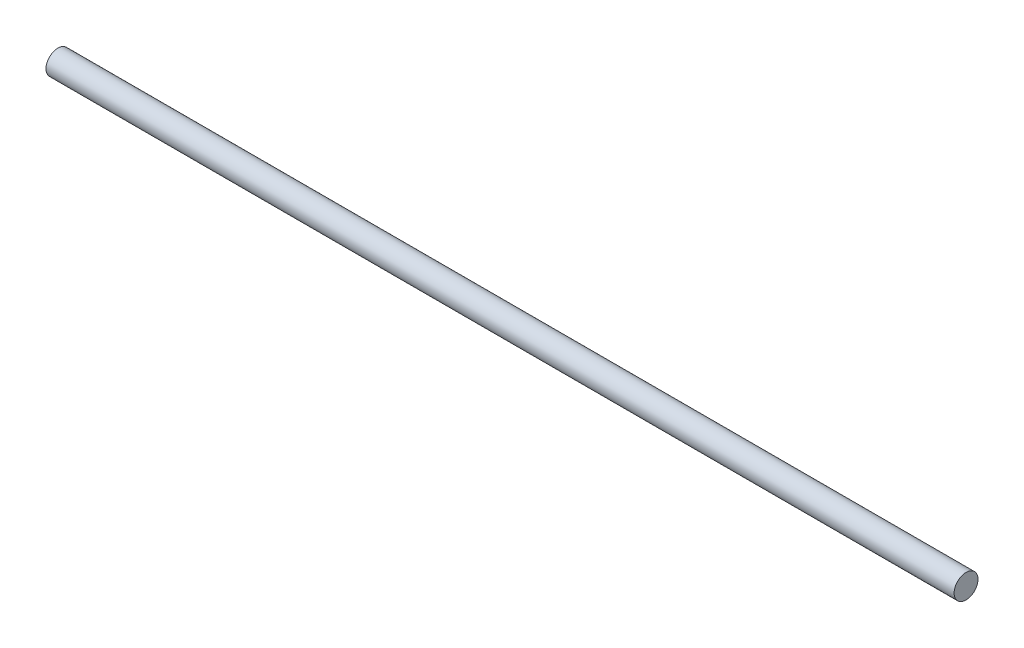
SolidWorks part; units mm, degrees
ref_plane "Front Plane" through (0, 0, 0) normal (0, 0, 1) x (1, 0, 0)
ref_plane "Top Plane" through (0, 0, 0) normal (0, 1, 0) x (1, 0, 0)
ref_plane "Right Plane" through (0, 0, 0) normal (1, 0, 0) x (0, 0, -1)
sketch "Sketch1" plane through (0, 0, 0) normal (1, 0, 0) x (0, 0, -1)
  circle A0 centre (0, 0) radius 4
  dimension "D1" = 8
extrude "Boss-Extrude1" add sketch "Sketch1" along normal mid plane 304
